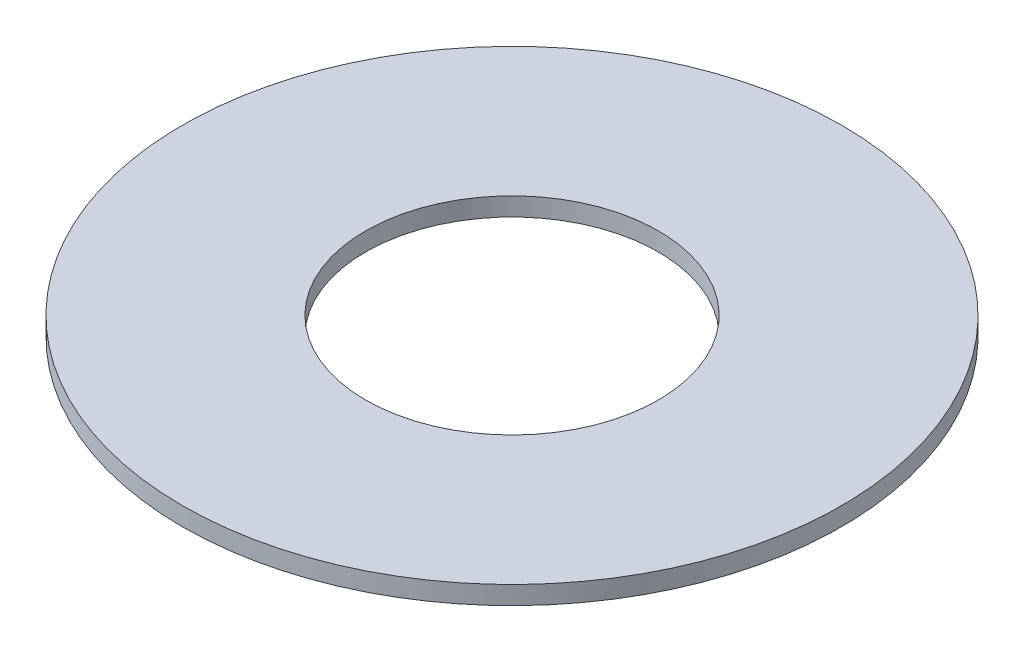
SolidWorks part; units mm, degrees
ref_plane "Front Plane" through (0, 0, 0) normal (0, 0, 1) x (1, 0, 0)
ref_plane "Top Plane" through (0, 0, 0) normal (0, 1, 0) x (1, 0, 0)
ref_plane "Right Plane" through (0, 0, 0) normal (1, 0, 0) x (0, 0, -1)
sketch "Sketch1" plane through (0, 0, 0) normal (0, 1, 0) x (1, 0, 0)
  circle A0 centre (0, 0) radius 4
  circle A1 centre (0, 0) radius 9
  dimension "D1" = 8
  dimension "D2" = 18
extrude "Boss-Extrude1" add sketch "Sketch1" along normal blind 0.5
